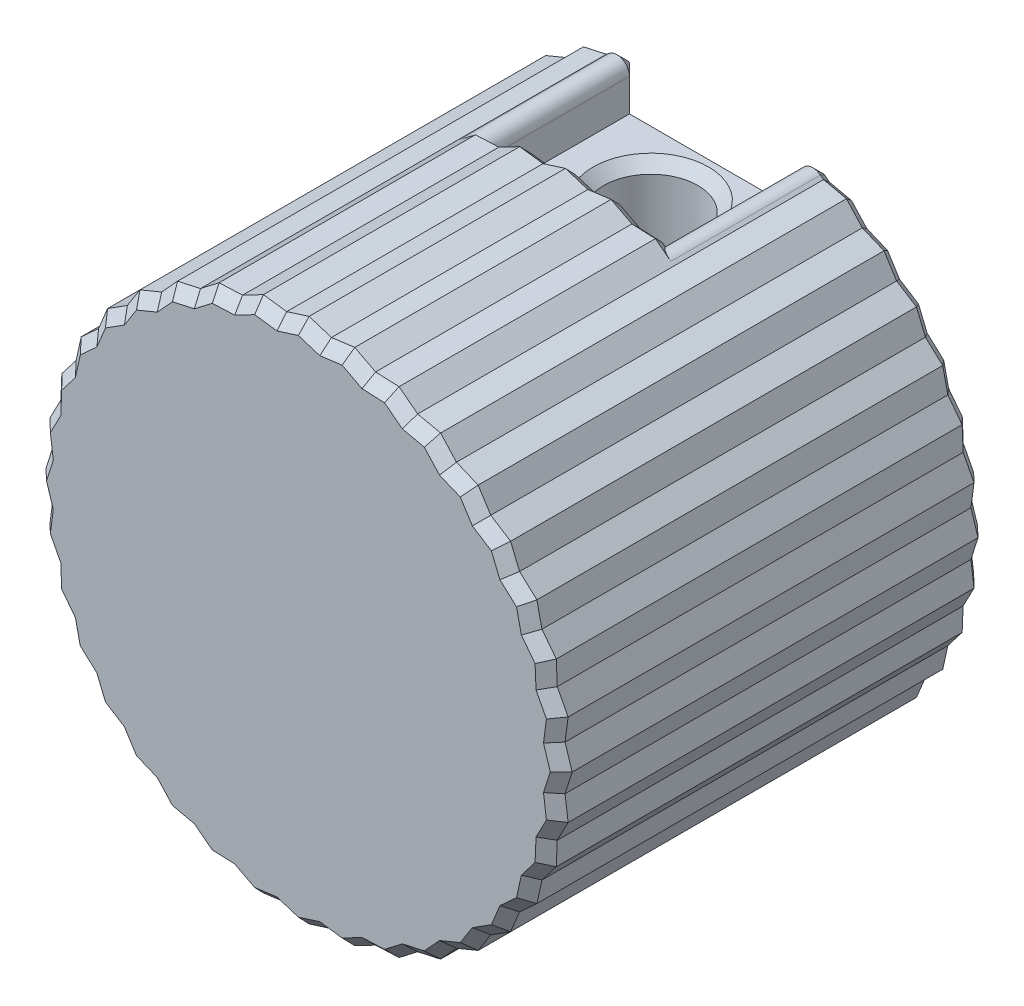
SolidWorks part; units mm, degrees
ref_plane "Front Plane (Z)" through (0, 0, 0) normal (0, 0, 1) x (1, 0, 0)
ref_plane "Top Plane (Y)" through (0, 0, 0) normal (0, 1, 0) x (1, 0, 0)
ref_plane "Side Plane (X)" through (0, 0, 0) normal (1, 0, 0) x (0, 0, -1)
sketch "Sketch1" plane through (0, 0, 0) normal (0, 0, 1) x (1, 0, 0)
  circle A0 centre (0, 0) radius 2.65
  circle A1 centre (0, 0) radius 12.025
  dimension "D1" = 5.3
  dimension "D2" = 24.05
extrude "Boss-Extrude1" add sketch "Sketch1" along normal blind 20
ref_plane "Plane1" through (0, 12.025, 0) normal (0, 1, 0) x (1, 0, 0)
sketch "Sketch5" plane through (0, 0, 0) normal (0, 0, -1) x (-1, 0, 0)
  line L0 (0, 0) -> (0, 13.8757) construction
  line L1 (0, 12.3158) -> (1.0485, 11.984)
  line L2 (0, 0) -> (1.0485, 11.984) construction
  line L3 (0, 12.3158) -> (-1.0485, 11.984)
  line L4 (2.1386, 12.1287) -> (1.0485, 11.984)
  line L5 (2.1386, 12.1287) -> (3.1135, 11.6199)
  line L6 (4.2123, 11.5731) -> (3.1135, 11.6199)
  line L7 (4.2123, 11.5731) -> (5.084, 10.9027)
  line L8 (6.1579, 10.6658) -> (5.084, 10.9027)
  line L9 (6.1579, 10.6658) -> (6.9, 9.8543)
  line L10 (7.9165, 9.4345) -> (6.9, 9.8543)
  line L11 (7.9165, 9.4345) -> (8.5064, 8.5064)
  line L12 (9.4345, 7.9165) -> (8.5064, 8.5064)
  line L13 (9.4345, 7.9165) -> (9.8543, 6.9)
  line L14 (10.6658, 6.1579) -> (9.8543, 6.9)
  line L15 (10.6658, 6.1579) -> (10.9027, 5.084)
  line L16 (11.5731, 4.2123) -> (10.9027, 5.084)
  line L17 (11.5731, 4.2123) -> (11.6199, 3.1135)
  line L18 (12.1287, 2.1386) -> (11.6199, 3.1135)
  line L19 (12.1287, 2.1386) -> (11.984, 1.0485)
  line L20 (12.3158, 0) -> (11.984, 1.0485)
  line L21 (12.3158, 0) -> (11.984, -1.0485)
  line L22 (12.1287, -2.1386) -> (11.984, -1.0485)
  line L23 (12.1287, -2.1386) -> (11.6199, -3.1135)
  line L24 (11.5731, -4.2123) -> (11.6199, -3.1135)
  line L25 (11.5731, -4.2123) -> (10.9027, -5.084)
  line L26 (10.6658, -6.1579) -> (10.9027, -5.084)
  line L27 (10.6658, -6.1579) -> (9.8543, -6.9)
  line L28 (9.4345, -7.9165) -> (9.8543, -6.9)
  line L29 (9.4345, -7.9165) -> (8.5064, -8.5064)
  line L30 (7.9165, -9.4345) -> (8.5064, -8.5064)
  line L31 (7.9165, -9.4345) -> (6.9, -9.8543)
  line L32 (6.1579, -10.6658) -> (6.9, -9.8543)
  line L33 (6.1579, -10.6658) -> (5.084, -10.9027)
  line L34 (4.2123, -11.5731) -> (5.084, -10.9027)
  line L35 (4.2123, -11.5731) -> (3.1135, -11.6199)
  line L36 (2.1386, -12.1287) -> (3.1135, -11.6199)
  line L37 (2.1386, -12.1287) -> (1.0485, -11.984)
  line L38 (0, -12.3158) -> (1.0485, -11.984)
  line L39 (0, -12.3158) -> (-1.0485, -11.984)
  line L40 (-2.1386, -12.1287) -> (-1.0485, -11.984)
  line L41 (-2.1386, -12.1287) -> (-3.1135, -11.6199)
  line L42 (-4.2123, -11.5731) -> (-3.1135, -11.6199)
  line L43 (-4.2123, -11.5731) -> (-5.084, -10.9027)
  line L44 (-6.1579, -10.6658) -> (-5.084, -10.9027)
  line L45 (-6.1579, -10.6658) -> (-6.9, -9.8543)
  line L46 (-7.9165, -9.4345) -> (-6.9, -9.8543)
  line L47 (-7.9165, -9.4345) -> (-8.5064, -8.5064)
  line L48 (-9.4345, -7.9165) -> (-8.5064, -8.5064)
  line L49 (-9.4345, -7.9165) -> (-9.8543, -6.9)
  line L50 (-10.6658, -6.1579) -> (-9.8543, -6.9)
  line L51 (-10.6658, -6.1579) -> (-10.9027, -5.084)
  line L52 (-11.5731, -4.2123) -> (-10.9027, -5.084)
  line L53 (-11.5731, -4.2123) -> (-11.6199, -3.1135)
  line L54 (-12.1287, -2.1386) -> (-11.6199, -3.1135)
  line L55 (-12.1287, -2.1386) -> (-11.984, -1.0485)
  line L56 (-12.3158, 0) -> (-11.984, -1.0485)
  line L57 (-12.3158, 0) -> (-11.984, 1.0485)
  line L58 (-12.1287, 2.1386) -> (-11.984, 1.0485)
  line L59 (-12.1287, 2.1386) -> (-11.6199, 3.1135)
  line L60 (-11.5731, 4.2123) -> (-11.6199, 3.1135)
  line L61 (-11.5731, 4.2123) -> (-10.9027, 5.084)
  line L62 (-10.6658, 6.1579) -> (-10.9027, 5.084)
  line L63 (-10.6658, 6.1579) -> (-9.8543, 6.9)
  line L64 (-9.4345, 7.9165) -> (-9.8543, 6.9)
  line L65 (-9.4345, 7.9165) -> (-8.5064, 8.5064)
  line L66 (-7.9165, 9.4345) -> (-8.5064, 8.5064)
  line L67 (-7.9165, 9.4345) -> (-6.9, 9.8543)
  line L68 (-6.1579, 10.6658) -> (-6.9, 9.8543)
  line L69 (-6.1579, 10.6658) -> (-5.084, 10.9027)
  line L70 (-4.2123, 11.5731) -> (-5.084, 10.9027)
  line L71 (-4.2123, 11.5731) -> (-3.1135, 11.6199)
  line L72 (-2.1386, 12.1287) -> (-3.1135, 11.6199)
  line L73 (-2.1386, 12.1287) -> (-1.0485, 11.984)
  circle A1 centre (0, 0) radius 11.6082
  point P116 (0, 0)
  dimension "D1" = 5
  dimension "D2" = 36
extrude "Boss-Extrude3" add sketch "Sketch5" against normal up to surface (20 mm away) up to face at (12.025, 0, 20)
sketch "Sketch3" plane through (0, 12.025, 0) normal (0, 1, 0) x (1, 0, 0)
  line L0 (0, 0) -> (0, -8.4013) construction
  line L2 (-4, 0) -> (4, 0)
  line L3 (4, 0) -> (4, -7)
  line L4 (4, -7) -> (-4, -7)
  line L5 (-4, 0) -> (-4, -7)
  circle A0 centre (0, -3.5) radius 3.15 construction
  point P11 (0, -7)
  dimension "D1" = 6.3
  dimension "D2" = 3.5
  dimension "D3" = 7
  dimension "D4" = 8
extrude "Cut-Extrude2" cut sketch "Sketch3" against normal blind 3 and the other way blind 2
sketch "Sketch2" plane through (0, 12.025, 0) normal (0, 1, 0) x (1, 0, 0)
  line L0 (0, 0) -> (0, -10.3234) construction
  line L2 (4, 0) -> (-4, 0) construction
  circle A0 centre (0, -3.5) radius 2.2
  dimension "D1" = 4.4
  dimension "D2" = 3.5
extrude "Cut-Extrude1" cut sketch "Sketch2" against normal up to next
sketch "Sketch4" plane through (0, 0, 20) normal (0, 0, 1) x (1, 0, 0)
  circle A0 centre (0, 0) radius 2.65
  circle A1 centre (0, 0) radius 2.65 construction
extrude "Boss-Extrude2" add sketch "Sketch4" against normal blind 2
sketch "Sketch7" plane through (0, 0, 0) normal (0, 0, -1) x (-1, 0, 0)
  line L0 (4, 11.5822) -> (4, 9.025) construction
  line L1 (5.084, 10.9027) -> (4.2123, 11.5731) construction
  line L2 (4, 10.5527) -> (4, 11.9105)
  line L3 (4, 11.9105) -> (4.9383, 11.0148)
  line L4 (0, 0) -> (0, 16.2537) construction
  line L5 (-4, 11.9105) -> (-4.9383, 11.0148)
  line L6 (-4, 10.5527) -> (-4, 11.9105)
  arc A0 (4, 10.5527) -> (4.9383, 11.0148) centre (4.5829, 10.5527) cw
  arc A1 (-4, 10.5527) -> (-4.9383, 11.0148) centre (-4.5829, 10.5527) ccw
extrude "Cut-Extrude3" cut sketch "Sketch7" against normal up to surface (7 mm away) up to face at (0, 11.3632, 7)
chamfer "Chamfer1" distance 0.5 angle 45 153 edges at (0.5242, 12.1499, 20) (-0.5242, 12.1499, 20) (-1.5935, 12.0564, 20) (-2.6261, 11.8743, 20) (-3.6629, 11.5965, 20) (-4.6481, 11.2379, 20) (-5.621, 10.7843, 20) (-6.529, 10.26, 20) (-7.4082, 9.6444, 20) (-8.2114, 8.9704, 20) (-8.9704, 8.2114, 20) (-9.6444, 7.4082, 20) (-10.26, 6.529, 20) (-10.7843, 5.621, 20) (-11.2379, 4.6481, 20) (-11.5965, 3.6629, 20) (-11.8743, 2.6261, 20) (-12.0564, 1.5935, 20) (-12.1499, 0.5242, 20) (-12.1499, -0.5242, 20) (-12.0564, -1.5935, 20) (-11.8743, -2.6261, 20) (1.5935, 12.0564, 7) (-11.5965, -3.6629, 20) (-11.2379, -4.6481, 20) (-10.7843, -5.621, 20) (-10.26, -6.529, 20) (-9.6444, -7.4082, 20) (-2.6261, 11.8743, 7) (-3.6629, 11.5965, 7) (3.6629, 11.5965, 7) (2.6261, 11.8743, 7) (0.5242, 12.1499, 7) (-0.5242, 12.1499, 7) (-1.5935, 12.0564, 7) (-8.9704, -8.2114, 20) (0, 9.025, 0) (-8.2114, -8.9704, 20) (-7.4082, -9.6444, 20) (-6.529, -10.26, 20) (-5.621, -10.7843, 20) (-4.6481, -11.2379, 20) (-3.6629, -11.5965, 20) (-2.6261, -11.8743, 20) (-1.5935, -12.0564, 20) (-0.5242, -12.1499, 20) (0, 9.025, 1.3) (0.5242, -12.1499, 20) (1.5935, -12.0564, 20) (2.6261, -11.8743, 20) (3.6629, -11.5965, 20) (4.6481, -11.2379, 20) (4, 9.7888, 0) (-4, 9.7888, 0) (5.621, -10.7843, 20) (5.0112, 10.9588, 0) (6.529, -10.26, 20) (7.4082, -9.6444, 20) (8.2114, -8.9704, 20) (-4.3254, 11.0756, 0) (8.9704, -8.2114, 20) (-4.5753, 11.294, 7) (9.6444, -7.4082, 20) (10.26, -6.529, 20) (10.7843, -5.621, 20) (4.3254, 11.0756, 0) (4.5753, 11.294, 7) (11.2379, -4.6481, 20) (11.5965, -3.6629, 20) (11.8743, -2.6261, 20) (12.0564, -1.5935, 20) (12.1499, -0.5242, 20) (12.1499, 0.5242, 20) (12.0564, 1.5935, 20) (11.8743, 2.6261, 20) (11.5965, 3.6629, 20) (11.2379, 4.6481, 20) (10.7843, 5.621, 20) (10.26, 6.529, 20) (9.6444, 7.4082, 20) (8.9704, 8.2114, 20) (8.2114, 8.9704, 20) (7.4082, 9.6444, 20) (6.529, 10.26, 20) (5.621, 10.7843, 20) (4.6481, 11.2379, 20) (3.6629, 11.5965, 20) (2.6261, 11.8743, 20) (1.5935, 12.0564, 20) (5.621, 10.7843, 0) (6.529, 10.26, 0) (7.4082, 9.6444, 0) (8.2114, 8.9704, 0) (8.9704, 8.2114, 0) (9.6444, 7.4082, 0) (10.26, 6.529, 0) (10.7843, 5.621, 0) (11.2379, 4.6481, 0) (11.5965, 3.6629, 0) (11.8743, 2.6261, 0) (12.0564, 1.5935, 0) (12.1499, 0.5242, 0) (12.1499, -0.5242, 0) (12.0564, -1.5935, 0) (11.8743, -2.6261, 0) (11.5965, -3.6629, 0) (11.2379, -4.6481, 0) (10.7843, -5.621, 0) (10.26, -6.529, 0) (9.6444, -7.4082, 0) (8.9704, -8.2114, 0) (8.2114, -8.9704, 0) (7.4082, -9.6444, 0) (6.529, -10.26, 0) (5.621, -10.7843, 0) (4.6481, -11.2379, 0) (3.6629, -11.5965, 0) (2.6261, -11.8743, 0) (1.5935, -12.0564, 0) (0.5242, -12.1499, 0) (-0.5242, -12.1499, 0) (-1.5935, -12.0564, 0) (-2.6261, -11.8743, 0) (-3.6629, -11.5965, 0) (-4.6481, -11.2379, 0) (-5.621, -10.7843, 0) (-6.529, -10.26, 0) (-7.4082, -9.6444, 0) (-8.2114, -8.9704, 0) (-8.9704, -8.2114, 0) (-9.6444, -7.4082, 0) (-10.26, -6.529, 0) (-10.7843, -5.621, 0) (-11.2379, -4.6481, 0) (-11.5965, -3.6629, 0) (-11.8743, -2.6261, 0) (-12.0564, -1.5935, 0) (-12.1499, -0.5242, 0) (-12.1499, 0.5242, 0) (-12.0564, 1.5935, 0) (-11.8743, 2.6261, 0) (-11.5965, 3.6629, 0) (-11.2379, 4.6481, 0) (-10.7843, 5.621, 0) (-10.26, 6.529, 0) (-9.6444, 7.4082, 0) (-8.9704, 8.2114, 0) (-8.2114, 8.9704, 0) (-7.4082, 9.6444, 0) (-6.529, 10.26, 0) (-5.621, 10.7843, 0) (-5.0112, 10.9588, 0) (2.65, 0, 0)
